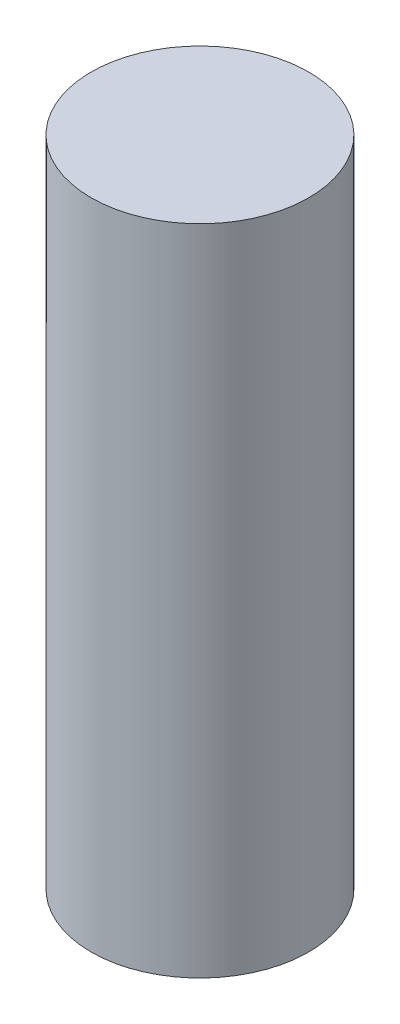
SolidWorks part; units mm, degrees
ref_plane "Front Plane" through (0, 0, 0) normal (0, 0, 1) x (1, 0, 0)
ref_plane "Top Plane" through (0, 0, 0) normal (0, 1, 0) x (1, 0, 0)
ref_plane "Right Plane" through (0, 0, 0) normal (1, 0, 0) x (0, 0, -1)
sketch "Sketch1" plane through (0, 0, 0) normal (0, 1, 0) x (1, 0, 0)
  circle A0 centre (0, 0) radius 2
  dimension "D1" = 4
extrude "Boss-Extrude1" add sketch "Sketch1" along normal blind 12
